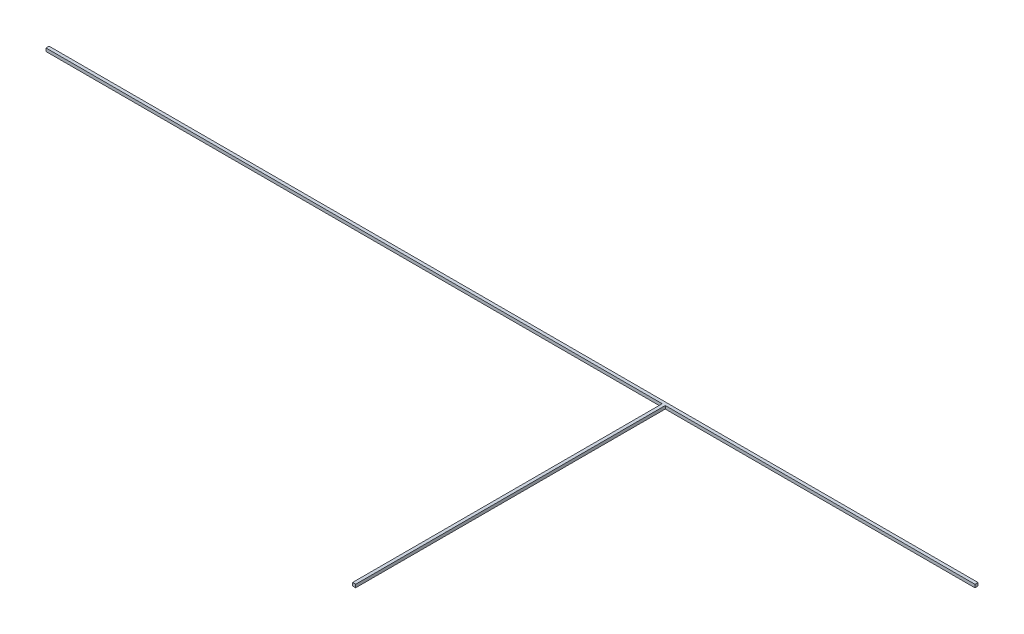
SolidWorks part; units mm, degrees
ref_plane "Front Plane" through (0, 0, 0) normal (0, 0, 1) x (1, 0, 0)
ref_plane "Top Plane" through (0, 0, 0) normal (0, 1, 0) x (1, 0, 0)
ref_plane "Right Plane" through (0, 0, 0) normal (1, 0, 0) x (0, 0, -1)
sketch "Sketch1" plane through (0, 0, 0) normal (1, 0, 0) x (0, 0, -1)
  line L1 (-0.3623, 0.442) -> (0.6377, 0.442)
  line L2 (-0.3623, 0.442) -> (-0.3623, -0.558)
  line L3 (-0.3623, -0.558) -> (0.6377, -0.558)
  line L4 (0.6377, 0.442) -> (0.6377, -0.558)
  dimension "D1" = 1
  dimension "D2" = 1
extrude "Boss-Extrude1" add sketch "Sketch1" along normal blind 300
sketch "Sketch2" plane through (0, 0, 0.3623) normal (0, 0, 1) x (1, 0, 0)
  line L0 (300, 0.442) -> (0, 0.442) construction
  line L1 (199, 0.442) -> (200, 0.442)
  line L2 (199, 0.442) -> (199, -0.558)
  line L3 (199, -0.558) -> (200, -0.558)
  line L4 (200, 0.442) -> (200, -0.558)
  line L5 (300, -0.558) -> (0, -0.558) construction
  line L6 (300, 0.442) -> (300, -0.558) construction
  dimension "D1" = 1
  dimension "D2" = 100
extrude "Boss-Extrude2" add sketch "Sketch2" along normal blind 100
